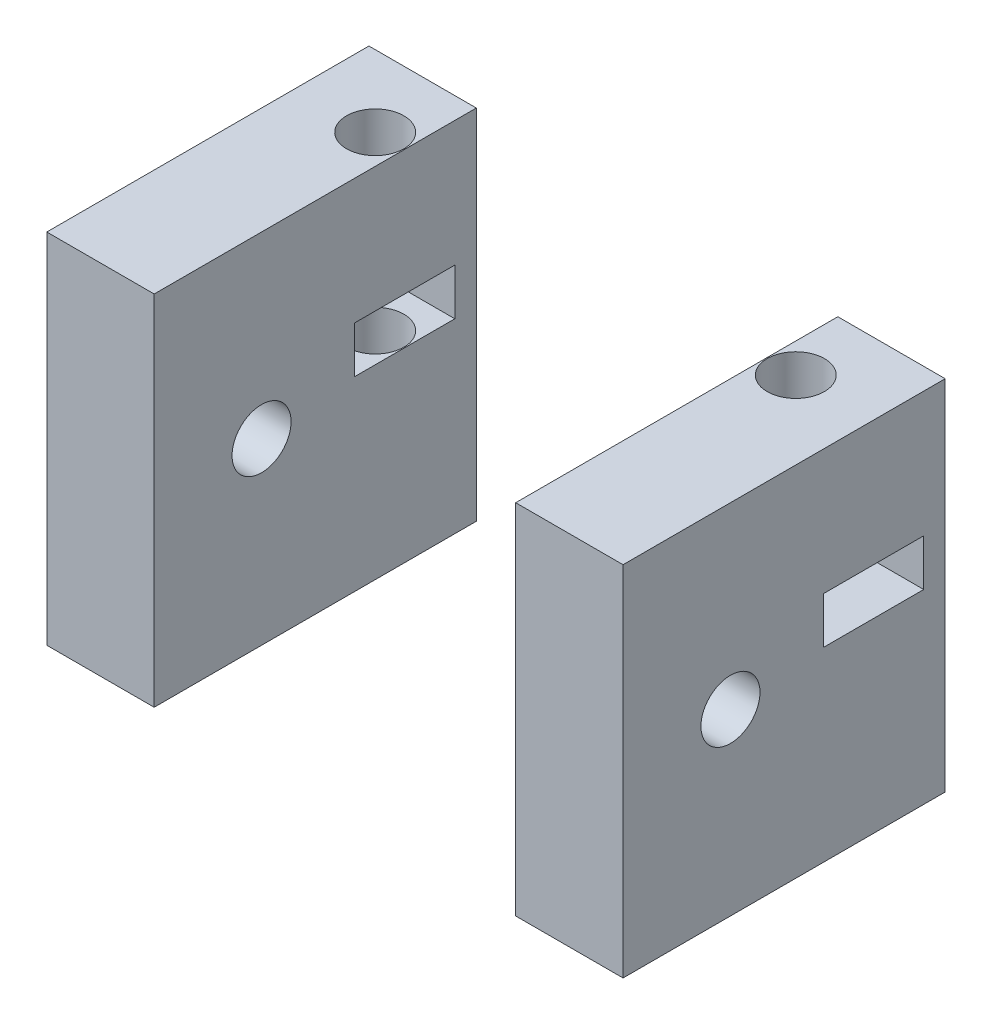
SolidWorks part; units mm, degrees
ref_plane "前视基准面" through (0, 0, 0) normal (0, 0, 1) x (1, 0, 0)
ref_plane "上视基准面" through (0, 0, 0) normal (0, 1, 0) x (1, 0, 0)
ref_plane "右视基准面" through (0, 0, 0) normal (1, 0, 0) x (0, 0, -1)
sketch "草图1" plane through (0, 0, 0) normal (0, 1, 0) x (1, 0, 0)
  line L0 (-11.75, 0) -> (11.75, 0) construction
  line L1 (-10.1, -10) -> (10.1, -10) construction
  line L2 (-10.1, -10) -> (-10.1, 10) construction
  line L3 (-10.1, 10) -> (10.1, 10) construction
  line L4 (10.1, -10) -> (10.1, 10) construction
  line L5 (-10.1, -10) -> (10.1, 10) construction
  line L6 (-10.1, 10) -> (10.1, -10) construction
  line L7 (-10.1, 4) -> (-16.1, 4)
  line L8 (-16.1, 4) -> (-16.1, -14)
  line L9 (-16.1, -14) -> (-10.1, -14)
  line L10 (-10.1, -14) -> (-10.1, 4)
  line L11 (0, 0) -> (0, 12.5739) construction
  line L12 (16.1, -14) -> (10.1, -14)
  line L13 (16.1, 4) -> (16.1, -14)
  line L14 (10.1, 4) -> (16.1, 4)
  line L15 (10.1, -14) -> (10.1, 4)
  circle A0 centre (-11.75, 0) radius 1.6
  circle A1 centre (11.75, 0) radius 1.6
  point P0 (0, 0)
  point P14 (0, 0)
  dimension "D3" = 3.2
  dimension "D1" = 20.2
  dimension "D2" = 20
  dimension "D4" = 23.5
  dimension "D5" = 6
  dimension "D6" = 18
  dimension "D7" = 4
extrude "凸台-拉伸1" add sketch "草图1" against normal blind 20
sketch "草图2" plane through (16.1, 0, 0) normal (1, 0, 0) x (0, 0, -1)
  line L0 (-14, 0) -> (4, 0) construction
  line L1 (-2.8, -7) -> (2.8, -7)
  line L2 (-2.8, -7) -> (-2.8, -9.6)
  line L3 (-2.8, -9.6) -> (2.8, -9.6)
  line L4 (2.8, -7) -> (2.8, -9.6)
  line L5 (-14, -20) -> (-14, 0) construction
  circle A0 centre (-8, -10) radius 1.65
  point P4 (0, -7)
  point P12 (-14, -10)
  dimension "D4" = 3.3
  dimension "D1" = 5.6
  dimension "D2" = 2.6
  dimension "D3" = 7
  dimension "D5" = 6
extrude "切除-拉伸1" cut sketch "草图2" against normal through all
